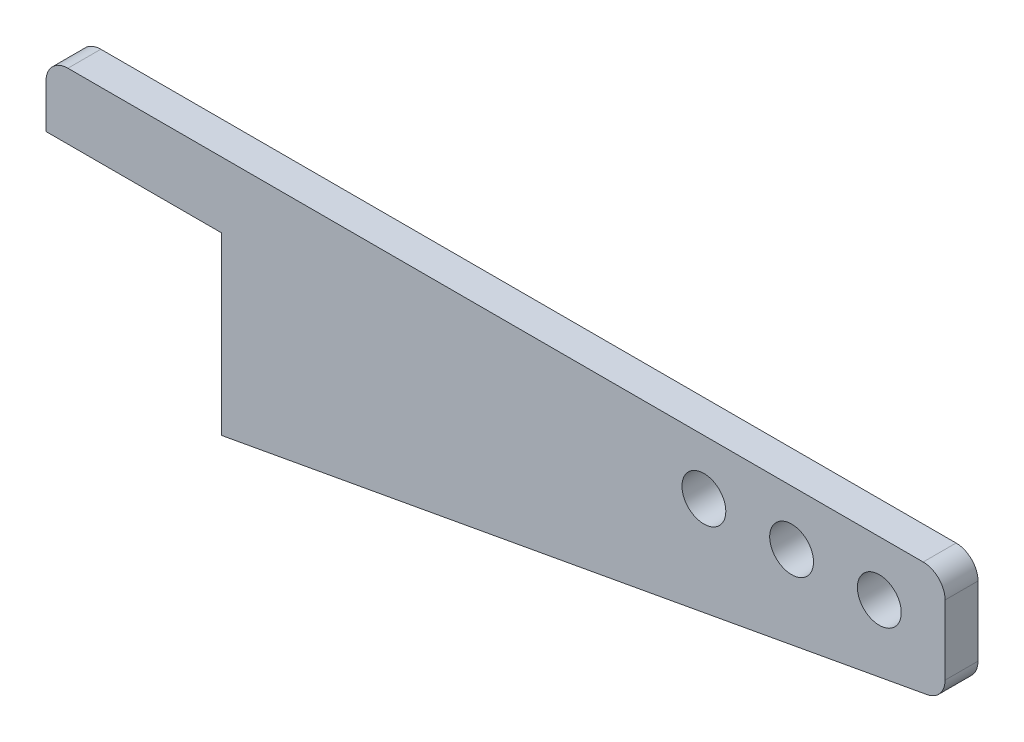
SolidWorks part; units mm, degrees
material "Acier non allié"
ref_plane "Plan de face" through (0, 0, 0) normal (0, 0, 1) x (1, 0, 0)
ref_plane "Plan de dessus" through (0, 0, 0) normal (0, 1, 0) x (1, 0, 0)
ref_plane "Plan de droite" through (0, 0, 0) normal (1, 0, 0) x (0, 0, -1)
sketch "Esquisse1" plane through (0, 0, 0) normal (0, 0, 1) x (1, 0, 0)
  line L0 (0, 0) -> (410, 0)
  line L1 (410, 0) -> (410, -50)
  line L2 (410, -50) -> (80, -110)
  line L3 (80, -110) -> (80, -30)
  line L4 (80, -30) -> (0, -30)
  line L5 (0, -30) -> (0, 0)
  line L6 (80, -110) -> (80, 0) construction
  line L7 (80, -25) -> (410, -25) construction
  circle A0 centre (300, -25) radius 10
  circle A1 centre (340, -25) radius 10
  circle A2 centre (380, -25) radius 10
  dimension "D6" = 20
  dimension "D1" = 410
  dimension "D2" = 50
  dimension "D3" = 110
  dimension "D4" = 80
  dimension "D5" = 80
  dimension "D7" = 40
  dimension "D8" = 40
  dimension "D9" = 30
extrude "Boss.-Extru.1" add sketch "Esquisse1" along normal blind 15
fillet "Congé1" radius 10 3 edges at (0, 0, 7.5) (410, -50, 7.5) (410, 0, 7.5)
